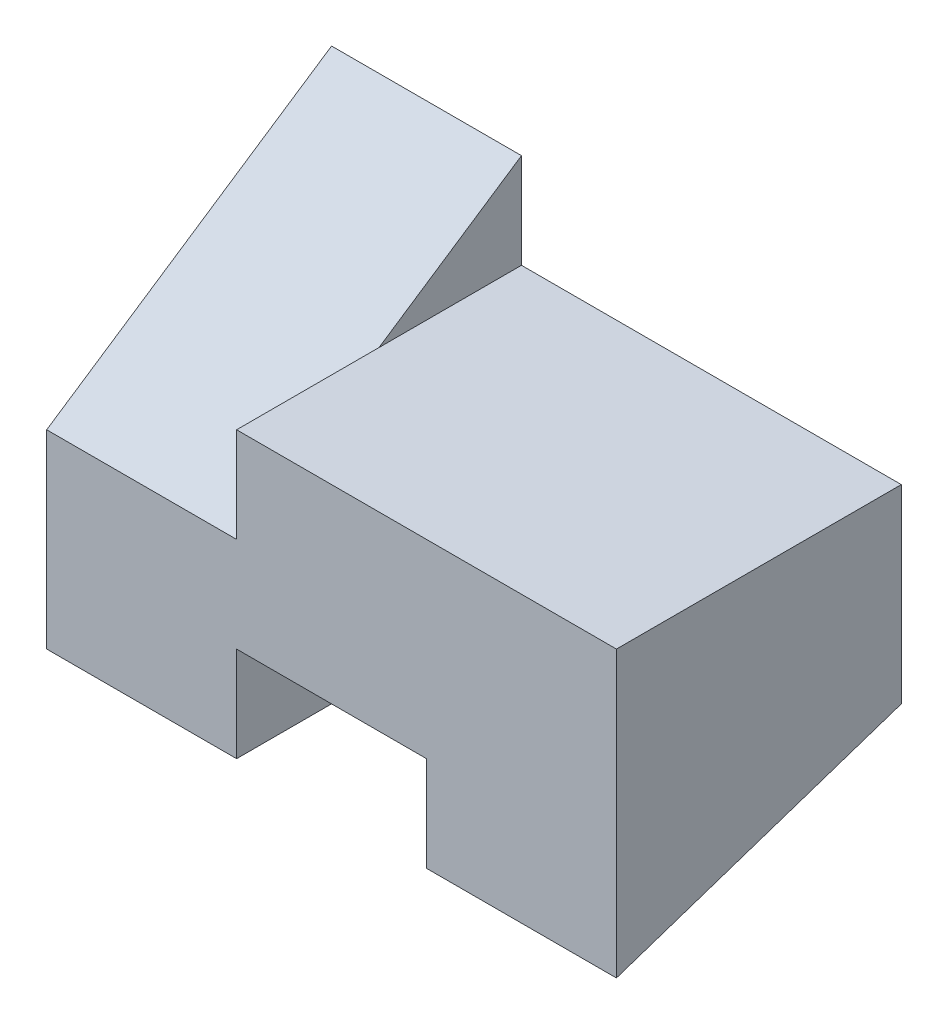
SolidWorks part; units mm, degrees
ref_plane "Front Plane" through (0, 0, 0) normal (0, 0, 1) x (1, 0, 0)
ref_plane "Top Plane" through (0, 0, 0) normal (0, 1, 0) x (1, 0, 0)
ref_plane "Right Plane" through (0, 0, 0) normal (1, 0, 0) x (0, 0, -1)
sketch "Sketch1" plane through (0, 0, 0) normal (0, 0, 1) x (1, 0, 0)
  line L0 (-20, -5) -> (-20, 5)
  line L1 (-20, 5) -> (-10, 5)
  line L2 (-10, 5) -> (-10, 10)
  line L3 (-10, 10) -> (0, 10)
  line L4 (0, 10) -> (0, 0)
  line L5 (0, 0) -> (-10, 0)
  line L6 (-10, 0) -> (-10, -5)
  line L7 (-10, -5) -> (-20, -5)
  dimension "D1" = 10
  dimension "D2" = 10
  dimension "D3" = 10
  dimension "D4" = 5
  dimension "D5" = 10
  dimension "D6" = 10
extrude "Boss-Extrude1" add sketch "Sketch1" along normal blind 15
sketch "Sketch2" plane through (-10, 0, 0) normal (1, 0, 0) x (0, 0, -1)
  line L1 (0, 0) -> (0, -5)
  line L3 (-15, 0) -> (0, -5)
  line L4 (-15, 0) -> (0, 0)
extrude "Boss-Extrude8" add sketch "Sketch2" along normal blind 10
sketch "Sketch5" plane through (0, 0, 0) normal (1, 0, 0) x (0, 0, -1)
  line L1 (-15, -5) -> (0, -5)
  line L2 (-15, -5) -> (-15, 10)
  line L3 (-15, 10) -> (0, 10)
  line L4 (0, -5) -> (0, 10)
extrude "Boss-Extrude10" add sketch "Sketch5" along normal blind 10
sketch "Sketch6" plane through (10, 0, 0) normal (1, 0, 0) x (0, 0, -1)
  line L2 (-15, -5) -> (0, 0)
  line L3 (-15, -5) -> (0, -5)
  line L4 (0, -5) -> (0, 0)
extrude "Cut-Extrude4" cut sketch "Sketch6" against normal blind 10
sketch "Sketch7" plane through (-10, 0, 0) normal (-1, 0, 0) x (0, 0, 1)
  line L0 (0, 5) -> (0, 15)
  line L1 (0, 15) -> (15, 5)
  line L2 (15, 5) -> (0, 5)
  dimension "D1" = 10
extrude "Boss-Extrude11" add sketch "Sketch7" along normal blind 10
